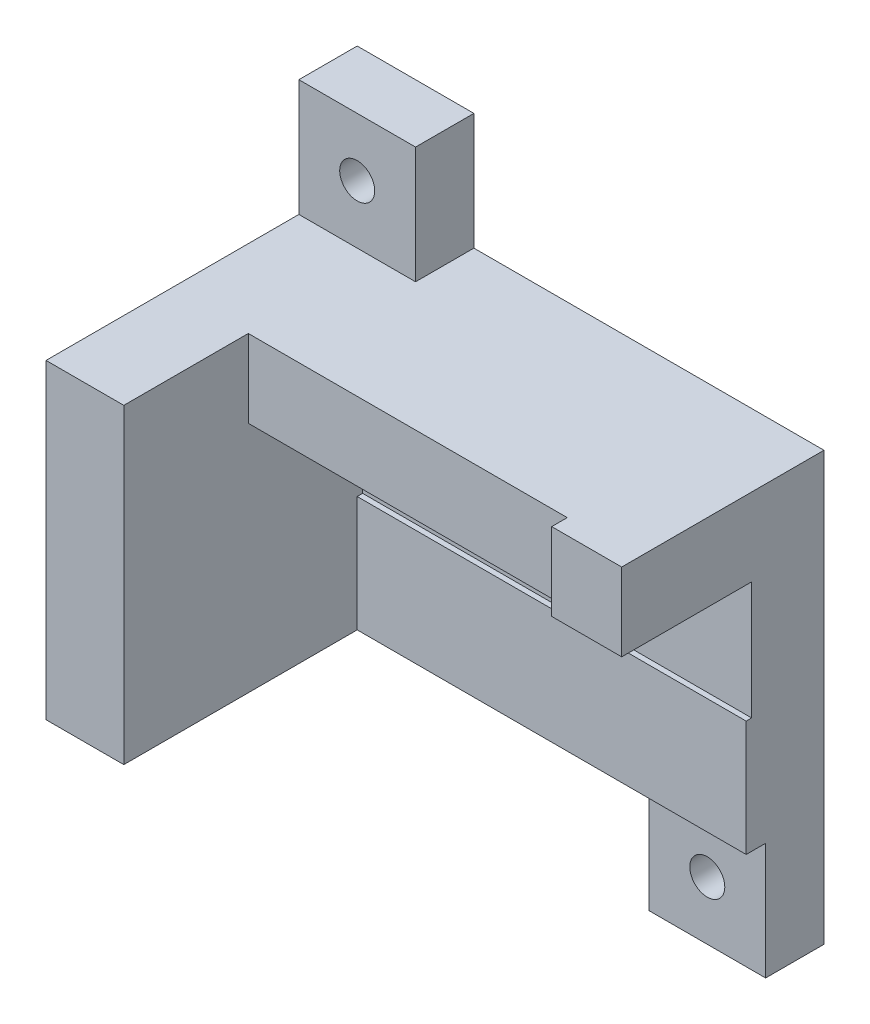
SolidWorks part; units mm, degrees
ref_plane "Front Plane" through (0, 0, 0) normal (0, 0, 1) x (1, 0, 0)
ref_plane "Top Plane" through (0, 0, 0) normal (0, 1, 0) x (1, 0, 0)
ref_plane "Right Plane" through (0, 0, 0) normal (1, 0, 0) x (0, 0, -1)
sketch "Sketch1" plane through (0, 0, 0) normal (0, 0, 1) x (1, 0, 0)
  line L0 (0, 0) -> (0, 40)
  line L1 (0, 40) -> (60, 40)
  line L2 (60, 40) -> (60, 0)
  line L3 (60, 0) -> (0, 0)
  dimension "D1" = 60
  dimension "D2" = 40
extrude "Boss-Extrude1" add sketch "Sketch1" along normal blind 40
sketch "Sketch2" plane through (0, 0, 40) normal (0, 0, 1) x (1, 0, 0)
  line L7 (10, 30) -> (60, 30)
  line L8 (10, 30) -> (10, 0)
  line L9 (10, 0) -> (60, 0)
  line L10 (60, 30) -> (60, 0)
  dimension "D1" = 50
  dimension "D2" = 30
extrude "Cut-Extrude1" cut sketch "Sketch2" against normal blind 30 contours L8 L7 L10 L9
sketch "Sketch3" plane through (0, 0, 10) normal (0, 0, 1) x (1, 0, 0)
  line L0 (60, 30) -> (60, 0) construction
  line L1 (10, 30) -> (60, 30)
  line L2 (10, 30) -> (10, 14.85)
  line L3 (10, 14.85) -> (60, 14.85)
  line L4 (60, 30) -> (60, 14.85)
  dimension "D1" = 15.15
extrude "Cut-Extrude2" cut sketch "Sketch3" against normal blind 0.7
sketch "Sketch4" plane through (0, 0, 40) normal (0, 0, 1) x (1, 0, 0)
  line L1 (10, 30) -> (60, 30)
  line L2 (10, 30) -> (10, 40)
  line L3 (10, 40) -> (60, 40)
  line L4 (60, 30) -> (60, 40)
extrude "Cut-Extrude3" cut sketch "Sketch4" against normal blind 14
sketch "Sketch5" plane through (0, 0, 26) normal (0, 0, 1) x (1, 0, 0)
  line L0 (60, 30) -> (10, 30) construction
  line L1 (10, 40) -> (51, 40)
  line L2 (10, 40) -> (10, 30)
  line L3 (10, 30) -> (51, 30)
  line L4 (51, 40) -> (51, 30)
  dimension "D1" = 41
extrude "Cut-Extrude4" cut sketch "Sketch5" against normal blind 2
sketch "Sketch6" plane through (0, 0, 0) normal (0, -1, 0) x (1, 0, 0)
  line L1 (60, 0) -> (45, 0)
  line L2 (60, 0) -> (60, 7.5)
  line L3 (60, 7.5) -> (45, 7.5)
  line L4 (45, 0) -> (45, 7.5)
  dimension "D1" = 15
  dimension "D2" = 7.5
extrude "Boss-Extrude3" add sketch "Sketch6" along normal blind 15
sketch "Sketch7" plane through (0, 40, 0) normal (0, 1, 0) x (1, 0, 0)
  line L1 (0, 0) -> (15, 0)
  line L2 (0, 0) -> (0, -7.5)
  line L3 (0, -7.5) -> (15, -7.5)
  line L4 (15, 0) -> (15, -7.5)
  dimension "D1" = 15
  dimension "D2" = 7.5
extrude "Boss-Extrude4" add sketch "Sketch7" along normal blind 15 contours L2 L1 L4 L3
sketch "Sketch8" plane through (0, 0, 7.5) normal (0, 0, 1) x (1, 0, 0)
  circle A0 centre (52.5, -7.5) radius 2.25
  circle A1 centre (7.5, 47.5) radius 2.25
  dimension "D1" = 4.5
  dimension "D2" = 4.5
extrude "Cut-Extrude5" cut sketch "Sketch8" against normal up to next
